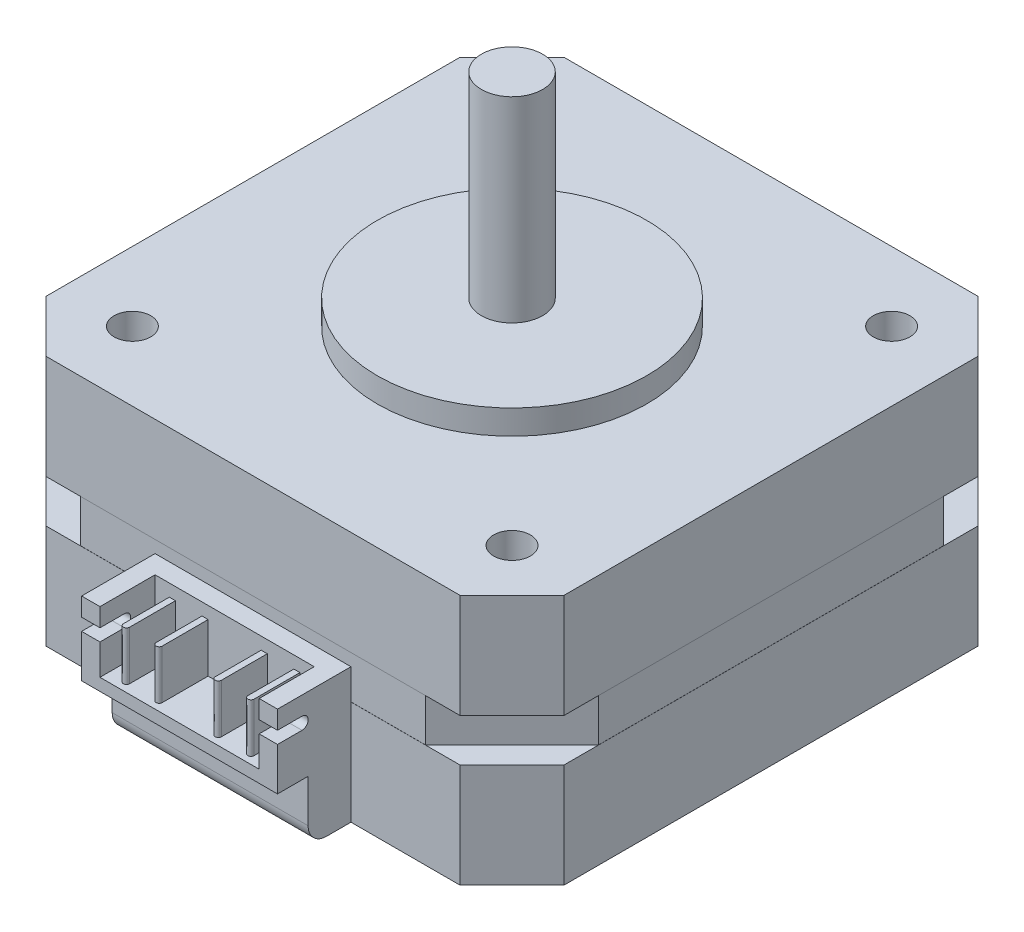
SolidWorks part; units mm, degrees
material "1060 Alloy"
ref_plane "Front Plane" through (0, 0, 0) normal (0, 0, 1) x (1, 0, 0)
ref_plane "Top Plane" through (0, 0, 0) normal (0, 1, 0) x (1, 0, 0)
ref_plane "Right Plane" through (0, 0, 0) normal (1, 0, 0) x (0, 0, -1)
sketch "Sketch1" plane through (0, 0, 0) normal (0, 1, 0) x (1, 0, 0)
  line L9 (-21.15, -21.15) -> (21.15, -21.15)
  line L10 (-21.15, -21.15) -> (-21.15, 21.15)
  line L11 (-21.15, 21.15) -> (21.15, 21.15)
  line L12 (21.15, -21.15) -> (21.15, 21.15)
  line L13 (-21.15, -21.15) -> (21.15, 21.15) construction
  line L14 (-21.15, 21.15) -> (21.15, -21.15) construction
  point P0 (0, 0)
  dimension "D1" = 42.3
extrude "Boss-Extrude1" add sketch "Sketch1" along normal blind 20.5
sketch "Sketch2" plane through (0, 20.5, 0) normal (0, 1, 0) x (1, 0, 0)
  circle A0 centre (0, 0) radius 11
  dimension "D1" = 22
extrude "Boss-Extrude2" add sketch "Sketch2" along normal blind 2
sketch "Sketch3" plane through (0, 22.5, 0) normal (0, 1, 0) x (1, 0, 0)
  circle A0 centre (0, 0) radius 2.5
  dimension "D1" = 5
extrude "Boss-Extrude3" add sketch "Sketch3" along normal blind 16
sketch "Sketch4" plane through (0, 20.5, 0) normal (0, 1, 0) x (1, 0, 0)
  line L0 (-21.15, 16.9074) -> (-16.9074, 21.15)
  line L1 (-21.15, 21.15) -> (-21.15, -21.15) construction
  line L2 (21.15, 21.15) -> (-21.15, 21.15) construction
  line L3 (-16.9074, 21.15) -> (-21.15, 21.15)
  line L4 (-21.15, 21.15) -> (-21.15, 16.9074)
  line L5 (0, 0) -> (0, 27.6659) construction
  line L6 (21.15, 21.15) -> (21.15, 16.9074)
  line L7 (16.9074, 21.15) -> (21.15, 21.15)
  line L8 (21.15, 16.9074) -> (16.9074, 21.15)
  line L9 (0, 0) -> (-36.313, 0) construction
  line L10 (21.15, -16.9074) -> (16.9074, -21.15)
  line L11 (16.9074, -21.15) -> (21.15, -21.15)
  line L12 (21.15, -21.15) -> (21.15, -16.9074)
  line L13 (-21.15, -21.15) -> (-21.15, -16.9074)
  line L14 (-16.9074, -21.15) -> (-21.15, -21.15)
  line L15 (-21.15, -16.9074) -> (-16.9074, -21.15)
  dimension "D1" = 45
  dimension "D2" = 6
extrude "Cut-Extrude1" cut sketch "Sketch4" against normal through all both and the other way through all
sketch "Sketch5" plane through (21.15, 0, 0) normal (1, 0, 0) x (0, 0, -1)
  line L0 (-16.9074, 0) -> (-16.9074, 20.5) construction
  line L1 (16.9074, 12) -> (-16.9074, 12)
  line L2 (16.9074, 12) -> (16.9074, 8.5)
  line L3 (16.9074, 8.5) -> (-16.9074, 8.5)
  line L4 (-16.9074, 12) -> (-16.9074, 8.5)
  line L5 (16.9074, 12) -> (-16.9074, 8.5) construction
  line L6 (16.9074, 8.5) -> (-16.9074, 12) construction
  line L7 (-16.9074, 0) -> (16.9074, 0) construction
  line L8 (-16.9074, 20.5) -> (16.9074, 20.5) construction
  line L9 (16.9074, 0) -> (16.9074, 20.5) construction
  point P0 (0, 10.25)
  dimension "D1" = 12
  dimension "D2" = 12
extrude "Cut-Extrude2" cut sketch "Sketch5" against normal blind 0.01
sketch "Sketch6" plane through (0, 20.5, 0) normal (0, 1, 0) x (1, 0, 0)
  line L0 (21.15, 14.0789) -> (14.0789, 21.15)
  line L1 (21.15, -16.9074) -> (21.15, 16.9074) construction
  line L2 (16.9074, 21.15) -> (-16.9074, 21.15) construction
  line L3 (14.0789, 21.15) -> (21.15, 21.15)
  line L4 (21.15, 21.15) -> (21.15, 14.0789)
  dimension "D1" = 10
  dimension "D2" = 45
extrude "Cut-Extrude3" cut sketch "Sketch6" against normal up to surface (3.5 mm away) from surface
pattern_circular "CirPattern1" count 4 over 360 about axis through (0, 0, 0) along (0, 1, 0) of "Cut-Extrude2", "Cut-Extrude3"
sketch "Sketch7" plane through (0, 20.5, 0) normal (0, 1, 0) x (1, 0, 0)
  circle A0 centre (15.5, 15.5) radius 1.5
  circle A1 centre (15.5, -15.5) radius 1.5
  circle A2 centre (-15.5, -15.5) radius 1.5
  circle A3 centre (-15.5, 15.5) radius 1.5
  point P12 (0, 0)
  dimension "D3" = 3
  dimension "D5" = 31
  dimension "D1" = 15.5
  dimension "D2" = 15.5
  dimension "D4" = 4
extrude "Cut-Extrude4" cut sketch "Sketch7" against normal blind 4.5
sketch "Sketch8" plane through (0, 0, 21.15) normal (0, 0, 1) x (1, 0, 0)
  line L0 (-16.9074, 0) -> (16.9074, 0) construction
  line L1 (-8, 0) -> (8, 0)
  line L2 (-8, 0) -> (-8, 11)
  line L3 (-8, 11) -> (8, 11)
  line L4 (8, 0) -> (8, 11)
  dimension "D1" = 16
  dimension "D2" = 11
extrude "Boss-Extrude4" add sketch "Sketch8" along normal blind 6
sketch "Sketch9" plane through (0, 0, 27.15) normal (0, 0, 1) x (1, 0, 0)
  line L0 (8, 0) -> (8, 8.5) construction
  line L1 (-8, 0) -> (8, 0)
  line L2 (-8, 0) -> (-8, 5)
  line L3 (-8, 5) -> (8, 5)
  line L4 (8, 0) -> (8, 5)
  dimension "D1" = 5
extrude "Cut-Extrude5" cut sketch "Sketch9" against normal blind 2.5
fillet "Fillet1" radius 1.5 1 edges at (0, 0, 24.65)
sketch "Sketch10" plane through (0, 11, 0) normal (0, 1, 0) x (1, 0, 0)
  line L0 (8, -27.15) -> (-8, -27.15) construction
  line L1 (-6.5, -27.15) -> (6.5, -27.15)
  line L2 (-6.5, -27.15) -> (-6.5, -22.65)
  line L3 (-6.5, -22.65) -> (6.5, -22.65)
  line L4 (6.5, -27.15) -> (6.5, -22.65)
  point P6 (0, -27.15)
  dimension "D1" = 13
  dimension "D2" = 4.5
extrude "Cut-Extrude6" cut sketch "Sketch10" against normal blind 5
sketch "Sketch11" plane through (8, 0, 0) normal (1, 0, 0) x (0, 0, -1)
  line L0 (-27.15, 5) -> (-27.15, 11) construction
  line L1 (-27.15, 11) -> (-21.15, 11) construction
  line L2 (-27.15, 9.5) -> (-25.15, 9.5)
  line L3 (-27.15, 9.5) -> (-27.15, 8.5)
  line L4 (-27.15, 8.5) -> (-25.15, 8.5)
  arc A0 (-25.15, 8.5) -> (-25.15, 9.5) centre (-25.15, 9) ccw
  point P5 (-24.65, 9)
  dimension "D2" = 1.5
  dimension "D1" = 1
extrude "Cut-Extrude7" cut sketch "Sketch11" against normal through all
sketch "Sketch12" plane through (0, 6, 0) normal (0, 1, 0) x (1, 0, 0)
  line L0 (0, 5.4741) -> (0, -32.9784) construction
  line L1 (6.5, -22.65) -> (-6.5, -22.65) construction
  line L2 (-2.667, -22.65) -> (-2.167, -22.65)
  line L3 (-2.667, -22.65) -> (-2.667, -26.4)
  line L5 (-2.167, -22.65) -> (-2.167, -26.4)
  line L8 (5.334, -22.65) -> (5.334, -26.4)
  line L9 (-4.834, -22.65) -> (-5.334, -22.65)
  line L10 (-4.834, -22.65) -> (-4.834, -26.4)
  line L12 (-5.334, -22.65) -> (-5.334, -26.4)
  line L13 (4.834, -22.65) -> (4.834, -26.4)
  line L14 (4.834, -22.65) -> (5.334, -22.65)
  line L15 (2.167, -22.65) -> (2.167, -26.4)
  line L16 (2.667, -22.65) -> (2.667, -26.4)
  line L17 (2.667, -22.65) -> (2.167, -22.65)
  arc A0 (-5.334, -26.4) -> (-4.834, -26.4) centre (-5.084, -26.4) ccw
  arc A1 (-2.667, -26.4) -> (-2.167, -26.4) centre (-2.417, -26.4) ccw
  arc A2 (2.667, -26.4) -> (2.167, -26.4) centre (2.417, -26.4) cw
  arc A3 (5.334, -26.4) -> (4.834, -26.4) centre (5.084, -26.4) cw
  point P4 (-2.417, -26.65)
  point P11 (-5.084, -26.65)
  dimension "D7" = 0.25
  dimension "D1" = 0.25
  dimension "D2" = 0.5
  dimension "D3" = 2.167
  dimension "D4" = 4
  dimension "D5" = 0.5
  dimension "D6" = 2.167
  dimension "D8" = 4
extrude "Boss-Extrude5" add sketch "Sketch12" along normal blind 4
